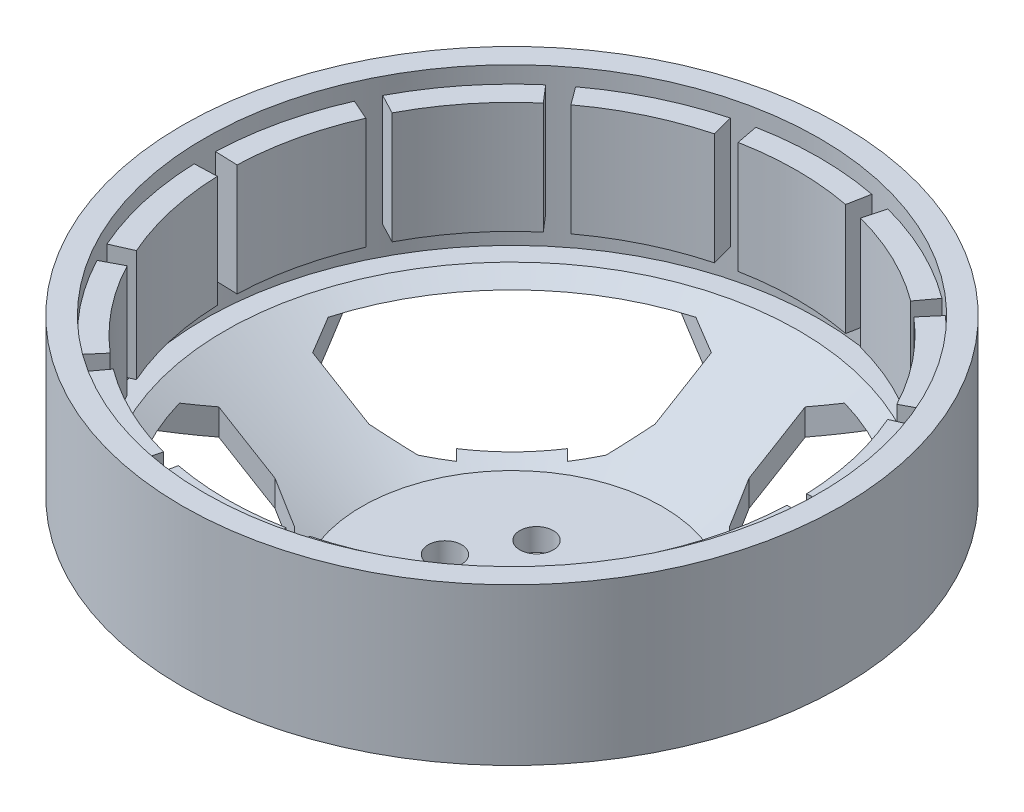
SolidWorks part; units mm, degrees
material "Stainless Steel (ferritic)"
ref_plane "Ön Düzlem" through (0, 0, 0) normal (0, 0, 1) x (1, 0, 0)
ref_plane "Üst Düzlem" through (0, 0, 0) normal (0, 1, 0) x (1, 0, 0)
ref_plane "Sağ Düzlem" through (0, 0, 0) normal (1, 0, 0) x (0, 0, -1)
sketch "Çizim1" plane through (0, 0, 0) normal (0, 1, 0) x (1, 0, 0)
  circle A0 centre (0, 0) radius 29.5
  circle A1 centre (0, 0) radius 27.5
  dimension "D1" = 59
  dimension "D2" = 2
extrude "Yükseklik-Ekstrüzyon1" add sketch "Çizim1" along normal blind 12
sketch "Çizim2" plane through (0, 0, 0) normal (0, 1, 0) x (1, 0, 0)
  line L0 (6.5305, 24.6496) -> (7.0427, 26.5829)
  line L1 (-4.8113, 25.042) -> (-5.1887, 27.0061)
  line L2 (4.8113, 25.042) -> (5.1887, 27.0061)
  line L3 (15.2002, 20.4745) -> (16.3923, 22.0803)
  line L4 (16.5788, 19.3751) -> (17.8791, 20.8947)
  line L5 (22.5784, 11.8518) -> (24.3493, 12.7813)
  line L6 (23.3435, 10.2631) -> (25.1744, 11.068)
  line L7 (25.4848, 0.8817) -> (27.4836, 0.9508)
  line L8 (25.4848, -0.8817) -> (27.4836, -0.9508)
  line L9 (23.3435, -10.2631) -> (25.1744, -11.068)
  line L10 (22.5784, -11.8518) -> (24.3493, -12.7813)
  line L11 (16.5788, -19.3751) -> (17.8791, -20.8947)
  line L12 (15.2002, -20.4745) -> (16.3923, -22.0803)
  line L13 (6.5305, -24.6496) -> (7.0427, -26.5829)
  line L14 (4.8113, -25.042) -> (5.1887, -27.0061)
  line L15 (-4.8113, -25.042) -> (-5.1887, -27.0061)
  line L16 (-6.5305, -24.6496) -> (-7.0427, -26.5829)
  line L17 (-15.2002, -20.4745) -> (-16.3923, -22.0803)
  line L18 (-16.5788, -19.3751) -> (-17.8791, -20.8947)
  line L19 (-22.5784, -11.8518) -> (-24.3493, -12.7813)
  line L20 (-23.3435, -10.2631) -> (-25.1744, -11.068)
  line L21 (-25.4848, -0.8817) -> (-27.4836, -0.9508)
  line L22 (-25.4848, 0.8817) -> (-27.4836, 0.9508)
  line L23 (-23.3435, 10.2631) -> (-25.1744, 11.068)
  line L24 (-22.5784, 11.8518) -> (-24.3493, 12.7813)
  line L25 (-16.5788, 19.3751) -> (-17.8791, 20.8947)
  line L26 (-15.2002, 20.4745) -> (-16.3923, 22.0803)
  line L27 (-6.5305, 24.6496) -> (-7.0427, 26.5829)
  arc A0 (4.8113, 25.042) -> (-4.8113, 25.042) centre (0, 0) ccw
  circle A2 centre (0, 0) radius 27.5 construction
  arc A3 (15.2002, 20.4745) -> (6.5305, 24.6496) centre (0, 0) ccw
  arc A4 (22.5784, 11.8518) -> (16.5788, 19.3751) centre (0, 0) ccw
  arc A5 (25.4848, 0.8817) -> (23.3435, 10.2631) centre (0, 0) ccw
  arc A6 (23.3435, -10.2631) -> (25.4848, -0.8817) centre (0, 0) ccw
  arc A7 (16.5788, -19.3751) -> (22.5784, -11.8518) centre (0, 0) ccw
  arc A8 (6.5305, -24.6496) -> (15.2002, -20.4745) centre (0, 0) ccw
  arc A9 (-4.8113, -25.042) -> (4.8113, -25.042) centre (0, 0) ccw
  arc A10 (-15.2002, -20.4745) -> (-6.5305, -24.6496) centre (0, 0) ccw
  arc A11 (-22.5784, -11.8518) -> (-16.5788, -19.3751) centre (0, 0) ccw
  arc A12 (-25.4848, -0.8817) -> (-23.3435, -10.2631) centre (0, 0) ccw
  arc A13 (-23.3435, 10.2631) -> (-25.4848, 0.8817) centre (0, 0) ccw
  arc A14 (-16.5788, 19.3751) -> (-22.5784, 11.8518) centre (0, 0) ccw
  arc A15 (-6.5305, 24.6496) -> (-15.2002, 20.4745) centre (0, 0) ccw
  arc A16 (-25.1744, 11.068) -> (-27.4836, 0.9508) centre (0, 0) ccw
  arc A17 (-7.0427, 26.5829) -> (-16.3923, 22.0803) centre (0, 0) ccw
  arc A18 (-7.0427, 26.5829) -> (-16.3923, 22.0803) centre (0, 0) ccw
  arc A19 (-17.8791, 20.8947) -> (-24.3493, 12.7813) centre (0, 0) ccw
  arc A20 (-17.8791, 20.8947) -> (-24.3493, 12.7813) centre (0, 0) ccw
  arc A21 (-25.1744, 11.068) -> (-27.4836, 0.9508) centre (0, 0) ccw
  arc A22 (-27.4836, -0.9508) -> (-25.1744, -11.068) centre (0, 0) ccw
  arc A23 (-27.4836, -0.9508) -> (-25.1744, -11.068) centre (0, 0) ccw
  arc A24 (-24.3493, -12.7813) -> (-17.8791, -20.8947) centre (0, 0) ccw
  arc A25 (-24.3493, -12.7813) -> (-17.8791, -20.8947) centre (0, 0) ccw
  arc A26 (-16.3923, -22.0803) -> (-7.0427, -26.5829) centre (0, 0) ccw
  arc A27 (-16.3923, -22.0803) -> (-7.0427, -26.5829) centre (0, 0) ccw
  arc A28 (-5.1887, -27.0061) -> (5.1887, -27.0061) centre (0, 0) ccw
  arc A29 (-5.1887, -27.0061) -> (5.1887, -27.0061) centre (0, 0) ccw
  arc A30 (7.0427, -26.5829) -> (16.3923, -22.0803) centre (0, 0) ccw
  arc A31 (7.0427, -26.5829) -> (16.3923, -22.0803) centre (0, 0) ccw
  arc A32 (17.8791, -20.8947) -> (24.3493, -12.7813) centre (0, 0) ccw
  arc A33 (17.8791, -20.8947) -> (24.3493, -12.7813) centre (0, 0) ccw
  arc A34 (25.1744, -11.068) -> (27.4836, -0.9508) centre (0, 0) ccw
  arc A35 (25.1744, -11.068) -> (27.4836, -0.9508) centre (0, 0) ccw
  arc A36 (27.4836, 0.9508) -> (25.1744, 11.068) centre (0, 0) ccw
  arc A37 (27.4836, 0.9508) -> (25.1744, 11.068) centre (0, 0) ccw
  arc A38 (24.3493, 12.7813) -> (17.8791, 20.8947) centre (0, 0) ccw
  arc A39 (24.3493, 12.7813) -> (17.8791, 20.8947) centre (0, 0) ccw
  arc A40 (16.3923, 22.0803) -> (7.0427, 26.5829) centre (0, 0) ccw
  arc A41 (16.3923, 22.0803) -> (7.0427, 26.5829) centre (0, 0) ccw
  arc A42 (5.1887, 27.0061) -> (-5.1887, 27.0061) centre (0, 0) ccw
  arc A43 (5.1887, 27.0061) -> (-5.1887, 27.0061) centre (0, 0) ccw
  point P65 (0, 0)
  dimension "D1" = 2
  dimension "D2" = 14
extrude "Yükseklik-Ekstrüzyon3" add sketch "Çizim2" along normal blind 10 from offset 0.5 contours L2 A42 L1 A0 | L27 A17 L26 A15 | L25 A19 L24 A14 | L23 A16 L22 A13 | L21 A22 L20 A12 | L19 A24 L18 A11 | L17 A26 L16 A10 | L15 A28 L14 A9 | L13 A30 L12 A8 | L11 A32 L10 A7 | L9 A34 L8 A6 | L7 A36 L6 A5 | L5 A38 L4 A4 | L3 A40 L0 A3
sketch "Çizim3" plane through (0, 0, 0) normal (0, -1, 0) x (1, 0, 0)
  circle A0 centre (0, 0) radius 29.5
  circle A1 centre (0, 0) radius 27.5
extrude "Yükseklik-Ekstrüzyon4" add sketch "Çizim3" along normal blind 2
sketch3d "3B Çizim3"
  line L0 (0, -2, 0) -> (29.5, -2, 0)
  line L1 (0, -2, 0) -> (0, -11.5, 0)
  line L2 (0, -11.5, 0) -> (14, -11.5, 0)
  line L3 (14, -11.5, 0) -> (29.5, -2, 0)
  line L4 (0, 12, 0) -> (0, -2, 0) construction
  circle A1 centre (0, -2, 0) radius 29.5 construction
  point P7 (0, -31.5, 0)
  dimension "D1" = 9.5
  dimension "D2" = 14
ref_plane "Düzlem1" through (0, 0, 0) normal (0, 0, -1) x (-1, 0, 0)
sketch "Çizim6" plane through (0, 0, 0) normal (0, 0, -1) x (-1, 0, 0)
  line L0 (-29.5, -2) -> (0, -2)
  line L1 (0, -2) -> (0, -11.5)
  line L2 (0, -11.5) -> (-14, -11.5)
  line L3 (-14, -11.5) -> (-29.5, -2)
  line L4 (0, -2) -> (0, -43.9758) construction
  line L5 (0, -9.5) -> (-13.4359, -9.5)
  line L6 (-13.4359, -9.5) -> (-25.6727, -2)
  line L7 (-29.5, -2) -> (-25.6727, -2)
  line L8 (-13.4359, -9.5) -> (-28.4549, -0.2948) construction
  dimension "D1" = 2
revolve "Döndür1" add sketch "Çizim6" angle 360 about L4
sketch "Sketch2" plane through (0, -11.5, 0) normal (0, -1, 0) x (1, 0, 0)
  line L0 (0, 29.5) -> (0, -29.5) construction
  line L1 (-29.5, 0) -> (29.5, 0) construction
  line L2 (0, 24.75) -> (10, 27.7534)
  line L3 (0, 24.75) -> (0, 29.5)
  line L4 (4.2, 22.0371) -> (4.2, 17)
  line L5 (4.2, 22.0371) -> (13.6626, 26.1454)
  line L6 (4.2, 17) -> (5.5265, 13.9448)
  line L7 (0, 0) -> (20.8597, 20.8597) construction
  line L8 (17, 4.2) -> (13.9448, 5.5265)
  line L9 (22.0371, 4.2) -> (26.1454, 13.6626)
  line L10 (22.0371, 4.2) -> (17, 4.2)
  line L11 (24.75, 0) -> (29.5, 0)
  line L12 (24.75, 0) -> (27.7534, 10)
  line L13 (5.5265, 13.9448) -> (7.2608, 12.2105)
  line L14 (7.2608, 12.2105) -> (7.798, 12.7478)
  line L15 (7.798, 12.7478) -> (12.7478, 7.798)
  line L16 (13.9448, 5.5265) -> (12.2105, 7.2608)
  line L17 (12.2105, 7.2608) -> (12.7478, 7.798)
  circle A0 centre (0, 0) radius 29.5 construction
  arc A1 (0, 29.5) -> (10, 27.7534) centre (0, 0) cw
  circle A2 centre (0, 0) radius 14 construction
  arc A3 (29.5, 0) -> (27.7534, 10) centre (0, 0) ccw
  arc A4 (13.6626, 26.1454) -> (26.1454, 13.6626) centre (0, 0) cw
  point P29 (10.2729, 10.2729)
  dimension "D7" = 1
  dimension "D1" = 4.75
  dimension "D2" = 10
  dimension "D3" = 4.2
  dimension "D4" = 5
  dimension "D5" = 3
  dimension "D6" = 4
  dimension "D8" = 45
  dimension "D9" = 3.5
extrude "Cut-Extrude2" cut sketch "Sketch2" against normal blind 8.5
pattern_circular "CirPattern1" count 4 over 360 about axis through (0, 0, 0) along (0, 1, 0) of "Cut-Extrude2"
sketch "Çizim10" plane through (0, -11.5, 0) normal (0, -1, 0) x (1, 0, 0)
  line L0 (2, 0) -> (14, 0) construction
  line L1 (0, 0) -> (0, 11.7171) construction
  circle A0 centre (0, 0) radius 2
  circle A1 centre (0, 0) radius 14 construction
  circle A2 centre (6, 0) radius 1.5
  circle A3 centre (-6, 0) radius 1.5
  circle A4 centre (-3, 5.1962) radius 1.5
  circle A5 centre (3, 5.1962) radius 1.5
  circle A6 centre (6, 0) radius 1.5
  circle A7 centre (3, -5.1962) radius 1.5
  circle A8 centre (-3, -5.1962) radius 1.5
  point P25 (0, 0)
  dimension "D1" = 4
  dimension "D3" = 3
  dimension "D2" = 6
  dimension "D4" = 6
extrude "Kes-Ekstrüzyon2" cut sketch "Çizim10" against normal up to next and the other way through all contours A3 | A4 | A5 | A2 | A7 | A8 | A0
